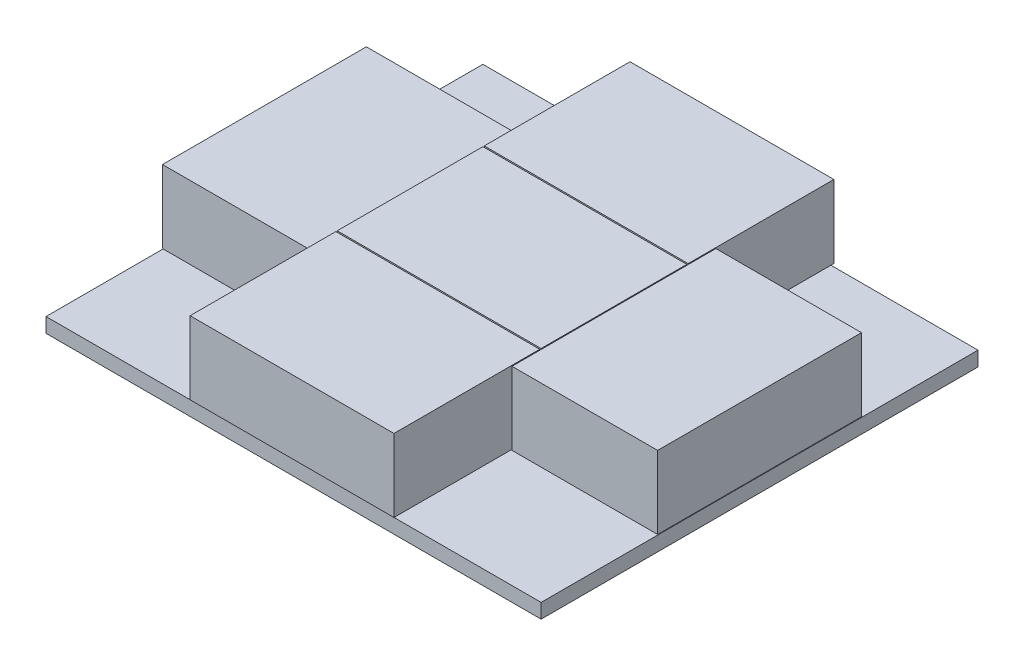
SolidWorks part; units mm, degrees
ref_plane "Front Plane" through (0, 0, 0) normal (0, 0, 1) x (1, 0, 0)
ref_plane "Top Plane" through (0, 0, 0) normal (0, 1, 0) x (1, 0, 0)
ref_plane "Right Plane" through (0, 0, 0) normal (1, 0, 0) x (0, 0, -1)
sketch "Sketch1" plane through (0, 0, 0) normal (0, 1, 0) x (1, 0, 0)
  line L1 (-85, -75) -> (85, -75)
  line L2 (-85, -75) -> (-85, 75)
  line L3 (-85, 75) -> (85, 75)
  line L4 (85, -75) -> (85, 75)
  line L5 (-85, -75) -> (85, 75) construction
  line L6 (-85, 75) -> (85, -75) construction
  point P0 (0, 0)
  dimension "D1" = 170
  dimension "D2" = 150
extrude "Boss-Extrude1" add sketch "Sketch1" along normal blind 5
sketch "Sketch4" plane through (0, 5, 0) normal (0, 1, 0) x (1, 0, 0)
  line L1 (-32.5, -22.5) -> (32.5, -22.5)
  line L2 (-32.5, -22.5) -> (-32.5, 22.5)
  line L3 (-32.5, 22.5) -> (32.5, 22.5)
  line L4 (32.5, -22.5) -> (32.5, 22.5)
  line L5 (-32.5, -22.5) -> (32.5, 22.5) construction
  line L6 (-32.5, 22.5) -> (32.5, -22.5) construction
  point P1 (0, 0)
  dimension "D1" = 65
  dimension "D2" = 45
extrude "Boss-Extrude2" add sketch "Sketch4" along normal blind 0.5
sketch "Sketch5" plane through (0, 5.5, 0) normal (0, 1, 0) x (1, 0, 0)
  line L1 (-35, -25.0221) -> (35, -25.0221)
  line L2 (-35, -25.0221) -> (-35, 25.0221)
  line L3 (-35, 25.0221) -> (35, 25.0221)
  line L4 (35, -25.0221) -> (35, 25.0221)
  line L5 (-35, -25.0221) -> (35, 25.0221) construction
  line L6 (-35, 25.0221) -> (35, -25.0221) construction
  point P0 (0, 0)
  dimension "D1" = 50.0441
  dimension "D2" = 70
extrude "Boss-Extrude3" add sketch "Sketch5" along normal blind 25
pattern_linear "LPattern3" count 2 spacing 50.5 along (0, 0, 1) count 2 spacing 50.5 along (0, 0, -1) of "Boss-Extrude2", "Boss-Extrude3"
sketch "Sketch6" plane through (0, 5, 0) normal (0, 1, 0) x (1, 0, 0)
  line L0 (0, 0) -> (128.1815, 0) construction
  line L1 (128.1815, 0) -> (0, 0) construction
  line L2 (0, 0) -> (-115.5479, 0) construction
  line L3 (32.5, -22.5) -> (32.5, 22.5) construction
  line L4 (37.5, -32.5) -> (82.5, -32.5)
  line L5 (37.5, -32.5) -> (37.5, 32.5)
  line L6 (37.5, 32.5) -> (82.5, 32.5)
  line L7 (82.5, -32.5) -> (82.5, 32.5)
  line L8 (37.5, -32.5) -> (82.5, 32.5) construction
  line L9 (37.5, 32.5) -> (82.5, -32.5) construction
  point P4 (60, 0)
  dimension "D1" = 45
  dimension "D2" = 5
  dimension "D3" = 65
extrude "Boss-Extrude4" add sketch "Sketch6" along normal blind 0.2
sketch "Sketch7" plane through (0, 5.2, 0) normal (0, 1, 0) x (1, 0, 0)
  line L0 (37.5, 32.5) -> (82.5, -32.5) construction
  line L1 (82.5, -32.5) -> (82.5, 32.5) construction
  line L2 (82.5, -32.5) -> (82.5, 32.5) construction
  line L3 (82.5, -32.5) -> (82.5, 32.5) construction
  line L4 (82.5, 32.5) -> (37.5, -32.5) construction
  line L6 (35, -35) -> (85, -35)
  line L7 (35, -35) -> (35, 35)
  line L8 (35, 35) -> (85, 35)
  line L9 (85, -35) -> (85, 35)
  line L10 (35, -35) -> (85, 35) construction
  line L11 (35, 35) -> (85, -35) construction
  point P7 (60, 0)
  dimension "D1" = 50
  dimension "D2" = 70
extrude "Boss-Extrude5" add sketch "Sketch7" along normal blind 25
pattern_linear "LPattern4" count 2 spacing 120 along (-1, 0, 0) of "Boss-Extrude4", "Boss-Extrude5"
